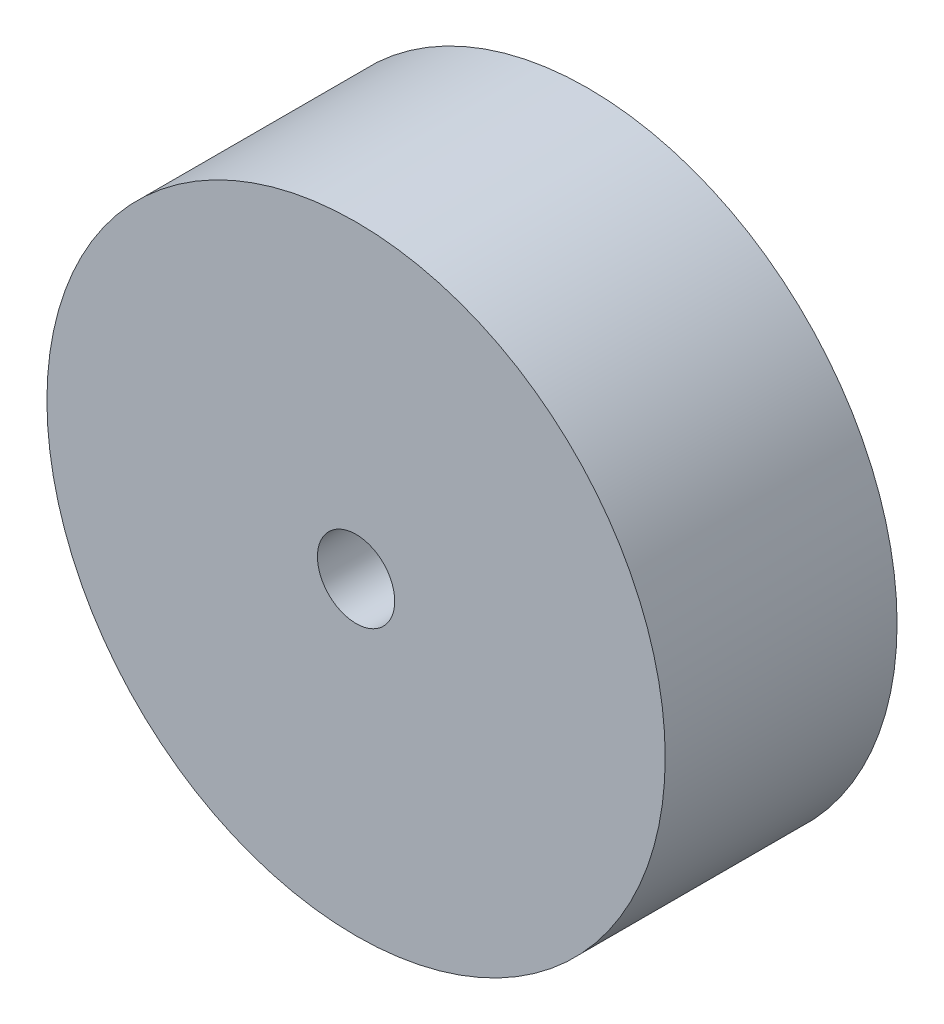
SolidWorks part; units mm, degrees
ref_plane "Front Plane" through (0, 0, 0) normal (0, 0, 1) x (1, 0, 0)
ref_plane "Top Plane" through (0, 0, 0) normal (0, 1, 0) x (1, 0, 0)
ref_plane "Right Plane" through (0, 0, 0) normal (1, 0, 0) x (0, 0, -1)
sketch "Sketch1" plane through (0, 0, 0) normal (0, 0, 1) x (1, 0, 0)
  circle A0 centre (0, 0) radius 101.6
  circle A1 centre (0, 0) radius 12.7
  dimension "D1" = 203.2
  dimension "D2" = 25.4
extrude "Boss-Extrude1" add sketch "Sketch1" along normal blind 76.2
